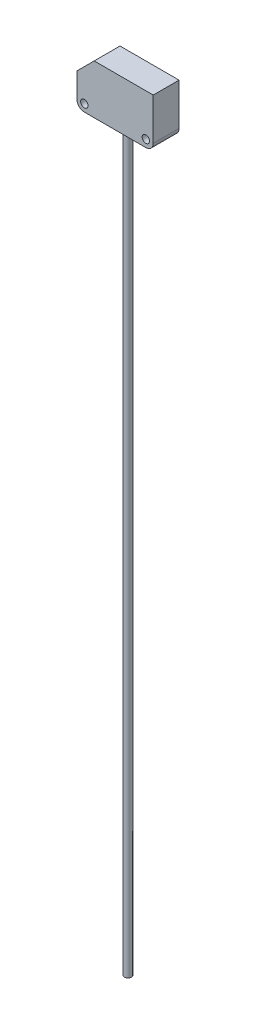
SolidWorks part; units mm, degrees
ref_plane "Plan de face" through (0, 0, 0) normal (0, 0, 1) x (1, 0, 0)
ref_plane "Plan de dessus" through (0, 0, 0) normal (0, 1, 0) x (1, 0, 0)
ref_plane "Plan de droite" through (0, 0, 0) normal (1, 0, 0) x (0, 0, -1)
sketch "Esquisse1" plane through (0, 0, 0) normal (0, 0, 1) x (1, 0, 0)
  line L0 (0, 0) -> (31, 0)
  line L1 (31, 0) -> (31, 20)
  line L2 (31, 20) -> (7, 20)
  line L3 (7, 20) -> (0, 13)
  line L4 (0, 13) -> (0, 0)
  dimension "D1" = 31
  dimension "D2" = 20
  dimension "D3" = 24
  dimension "D4" = 45
extrude "Boss.-Extru.1" add sketch "Esquisse1" against normal blind 10.5
sketch "Esquisse2" plane through (0, 0, 0) normal (0, 0, 1) x (1, 0, 0)
  line L0 (31, 0) -> (31, 20) construction
  line L1 (0, 0) -> (31, 0) construction
  line L2 (0, 13) -> (0, 0) construction
  circle A0 centre (3, 3) radius 1.5
  circle A1 centre (28, 3) radius 1.5
  dimension "D1" = 3
  dimension "D2" = 3
  dimension "D3" = 3
  dimension "D4" = 3
  dimension "D5" = 3
  dimension "D6" = 3
extrude "Enlèv. mat.-Extru.1" cut sketch "Esquisse2" against normal through all
fillet "Congé1" radius 3 2 edges at (31, 0, -5.25) (0, 0, -5.25)
sketch "Esquisse3" plane through (0, 0, 0) normal (0, -1, 0) x (1, 0, 0)
  line L0 (6.5, 0) -> (6.5, -10.5)
  line L1 (3, 0) -> (28, 0) construction
  line L2 (3, -10.5) -> (28, -10.5) construction
  line L3 (6.5, -10.5) -> (24.5, -10.5)
  line L4 (24.5, -10.5) -> (24.5, 0)
  line L5 (24.5, 0) -> (6.5, 0)
  line L6 (31, 0) -> (31, -10.5) construction
  dimension "D1" = 18
  dimension "D2" = 6.5
extrude "Boss.-Extru.2" add sketch "Esquisse3" along normal blind 0.01
sketch "Esquisse4" plane through (0, -0.01, 0) normal (0, -1, 0) x (1, 0, 0)
  line L0 (15.5, -10.5) -> (15.5, 0) construction
  line L1 (6.5, -10.5) -> (24.5, -10.5) construction
  line L2 (24.5, 0) -> (6.5, 0) construction
  circle A0 centre (15.5, -5.25) radius 1.5
  dimension "D1" = 3
extrude "Boss.-Extru.3" add sketch "Esquisse4" along normal blind 300
